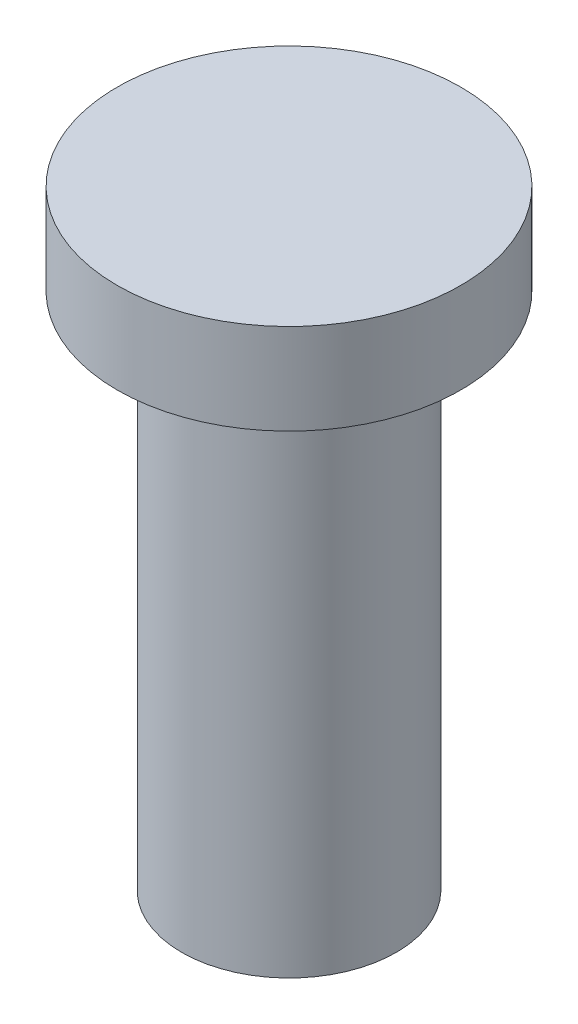
SolidWorks part; units mm, degrees
ref_plane "Front Plane" through (0, 0, 0) normal (0, 0, 1) x (1, 0, 0)
ref_plane "Top Plane" through (0, 0, 0) normal (0, 1, 0) x (1, 0, 0)
ref_plane "Right Plane" through (0, 0, 0) normal (1, 0, 0) x (0, 0, -1)
sketch "Sketch1" plane through (0, 0, 0) normal (0, 1, 0) x (1, 0, 0)
  circle A0 centre (0, 0) radius 3.9688
  dimension "D1" = 7.9375
extrude "Boss-Extrude1" add sketch "Sketch1" along normal blind 20
sketch "Sketch2" plane through (0, 0, 0) normal (0, -1, 0) x (1, 0, 0)
  circle A0 centre (0, 0) radius 1.675
  dimension "D1" = 3.35
extrude "Cut-Extrude1" cut sketch "Sketch2" against normal blind 12
sketch "Sketch4" plane through (0, 20, 0) normal (0, 1, 0) x (1, 0, 0)
  circle A0 centre (0, 0) radius 6.35
  dimension "D1" = 12.7
extrude "Boss-Extrude2" add sketch "Sketch4" along normal blind 2.54
sketch "Sketch6" plane through (0, 22.54, 0) normal (0, 1, 0) x (1, 0, 0)
  circle A0 centre (0, 0) radius 6.35
  dimension "D1" = 12.7
extrude "Boss-Extrude3" add sketch "Sketch6" against normal blind 3.35
